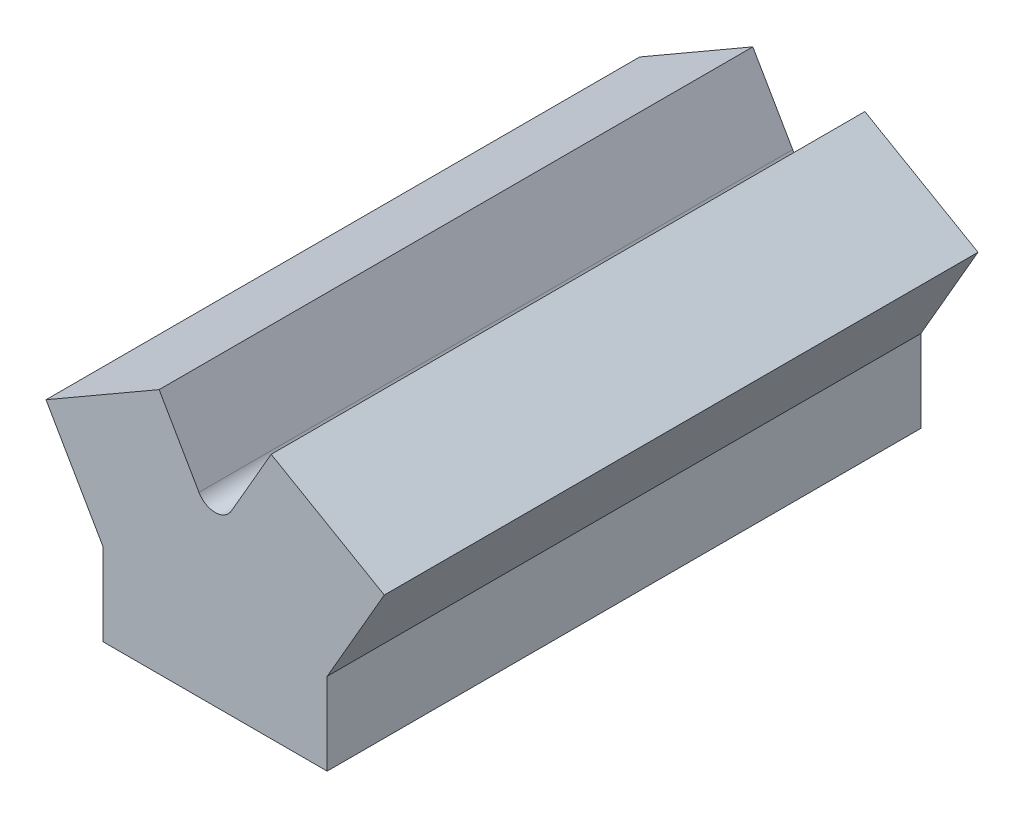
SolidWorks part; units mm, degrees
ref_plane "Front Plane" through (0, 0, 0) normal (0, 0, 1) x (1, 0, 0)
ref_plane "Top Plane" through (0, 0, 0) normal (0, 1, 0) x (1, 0, 0)
ref_plane "Right Plane" through (0, 0, 0) normal (1, 0, 0) x (0, 0, -1)
sketch "Sketch1" plane through (0, 0, 0) normal (0, 0, 1) x (1, 0, 0)
  line L0 (-10.9985, 120.65) -> (-38.1141, 167.6156)
  line L1 (-38.1141, 167.6156) -> (-115.0614, 123.19)
  line L2 (-115.0614, 123.19) -> (-76.2, 55.88)
  line L3 (-76.2, 55.88) -> (-76.2, 0)
  line L4 (-76.2, 0) -> (76.2, 0)
  line L5 (76.2, 0) -> (76.2, 55.88)
  line L6 (76.2, 55.88) -> (115.0614, 123.19)
  line L7 (115.0614, 123.19) -> (38.1141, 167.6156)
  line L8 (38.1141, 167.6156) -> (10.9985, 120.65)
  line L9 (0, 0) -> (0, 243.1365) construction
  circle A0 centre (0, 127) radius 12.7
  dimension "D1" = 25.4
  dimension "D5" = 60
  dimension "D2" = 127
  dimension "D3" = 55.88
  dimension "D4" = 152.4
  dimension "D6" = 123.19
  dimension "D7" = 76.2
extrude "Boss-Extrude1" add sketch "Sketch1" along normal blind 403.86 contours L4 L9 A0 L0 L1 L2 L3 | L9 L4 L5 L6 L7 L8 A0
sketch "Sketch2" plane through (82.1082, 142.2156, 0) normal (0.5, 0.866, 0) x (0.866, -0.5, 0)
  line L0 (-6.3744, -403.86) -> (-6.3744, 0) construction
  line L1 (38.0511, -403.86) -> (-50.8, -403.86) construction
  line L2 (38.0511, 0) -> (-50.8, 0) construction
  circle A0 centre (-6.3744, -284.48) radius 22.86
  circle A1 centre (-6.3744, -172.72) radius 22.86
  circle A2 centre (-6.3744, -60.96) radius 22.86
  dimension "D1" = 119.38
  dimension "D2" = 45.72
  dimension "D3" = 45.72
  dimension "D6" = 45.72
  dimension "D4" = 111.76
  dimension "D5" = 111.76
sketch "Sketch3" plane through (-82.1082, 142.2156, 0) normal (-0.5, 0.866, 0) x (0.866, 0.5, 0)
  line L0 (6.3744, -403.86) -> (6.3744, 0) construction
  line L1 (50.8, -403.86) -> (-38.0511, -403.86) construction
  line L2 (50.8, 0) -> (-38.0511, 0) construction
  circle A0 centre (6.3744, -340.36) radius 22.86
  circle A1 centre (6.3744, -228.6) radius 22.86
  circle A2 centre (6.3744, -116.84) radius 22.86
  dimension "D1" = 45.72
  dimension "D3" = 45.72
  dimension "D6" = 45.72
  dimension "D2" = 63.5
  dimension "D4" = 111.76
  dimension "D5" = 111.76
extrude "Cut-Extrude1" cut sketch "Sketch3" against normal blind 403.86 from offset 19.05 offset against normal yes
sketch "Sketch4" plane through (82.1082, 142.2156, 0) normal (0.5, 0.866, 0) x (0.866, -0.5, 0)
extrude "Cut-Extrude2" cut sketch "Sketch2" against normal blind 403.86 from offset 19.05 offset against normal yes
sketch "Sketch6" plane through (0, 0, 403.86) normal (0, 0, 1) x (1, 0, 0)
  line L0 (-76.2, 0) -> (76.2, 0) construction
  line L1 (50.8, 0) -> (50.8, 31.75)
  line L2 (50.8, 31.75) -> (26.3115, 45.814)
  line L3 (-50.8, 0) -> (-50.8, 31.75)
  line L4 (-50.8, 31.75) -> (-26.3115, 45.814)
  line L5 (-50.8, 0) -> (50.8, 0)
  line L6 (-76.2, 55.88) -> (-76.2, 0) construction
  arc A0 (26.3115, 45.814) -> (-26.3115, 45.814) centre (0, 0) ccw
  dimension "D1" = 105.664
  dimension "D2" = 31.75
  dimension "D3" = 25.4
extrude "Cut-Extrude3" cut sketch "Sketch6" against normal offset from surface (353.06 mm away) 25.4 from offset 25.4 up to face at (0, 92.8321, 0) offset against normal yes
sketch "Sketch7" plane through (0, 0, 0) normal (0, -1, 0) x (1, 0, 0)
  line L0 (-76.2, 403.86) -> (-76.2, 0) construction
  line L1 (76.2, 403.86) -> (76.2, 0) construction
  line L2 (-76.2, 403.86) -> (76.2, 403.86) construction
  line L3 (-76.2, 0) -> (76.2, 0) construction
  circle A0 centre (63.5, 391.16) radius 6.35
  circle A1 centre (-63.5, 12.7) radius 6.35
  dimension "D2" = 12.7
  dimension "D4" = 12.7
  dimension "D1" = 12.7
  dimension "D3" = 12.7
  dimension "D5" = 12.7
  dimension "D6" = 12.7
extrude "Cut-Extrude4" cut sketch "Sketch7" against normal blind 76.2
